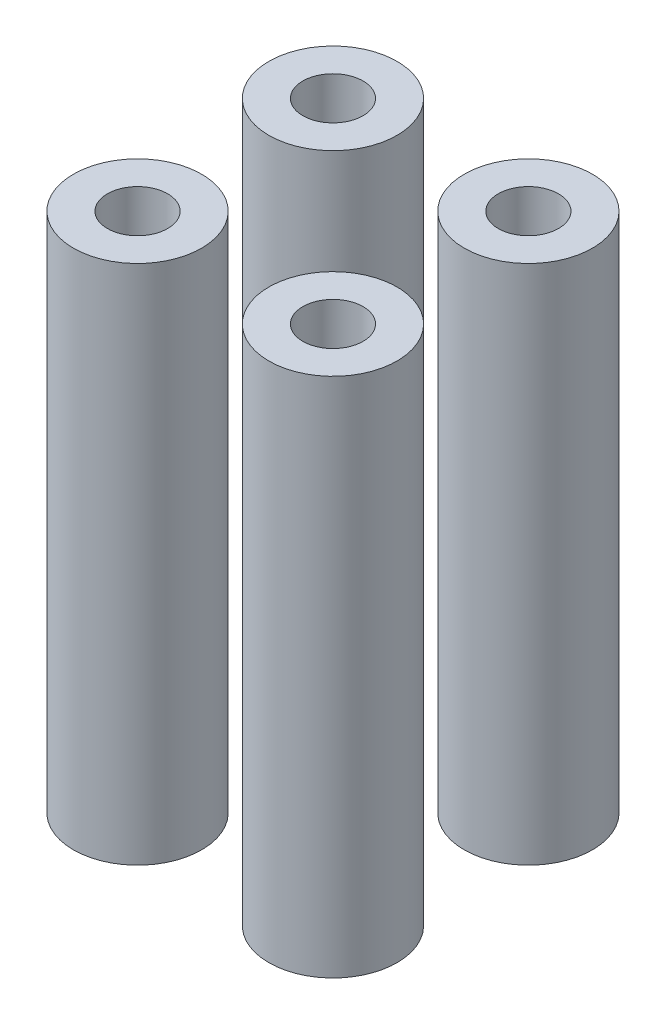
SolidWorks part; units mm, degrees
ref_plane "Front Plane" through (0, 0, 0) normal (0, 0, 1) x (1, 0, 0)
ref_plane "Top Plane" through (0, 0, 0) normal (0, 1, 0) x (1, 0, 0)
ref_plane "Right Plane" through (0, 0, 0) normal (1, 0, 0) x (0, 0, -1)
sketch "Sketch2" plane through (0, 0, 0) normal (0, 1, 0) x (1, 0, 0)
  circle A0 centre (0, 0) radius 2.5
  dimension "D1" = 5
extrude "Boss-Extrude2" add sketch "Sketch2" along normal blind 20.32
sketch "Sketch4" plane through (0, 20.32, 0) normal (0, 1, 0) x (1, 0, 0)
  circle A0 centre (0, 0) radius 1.175
  dimension "D1" = 2.35
extrude "Cut-Extrude1" cut sketch "Sketch4" against normal blind 6.35
pattern_linear "LPattern1" count 2 spacing 7.62 along (0, 0, 1) count 2 spacing 7.62 along (1, 0, 0) of "Boss-Extrude2", "Cut-Extrude1"
